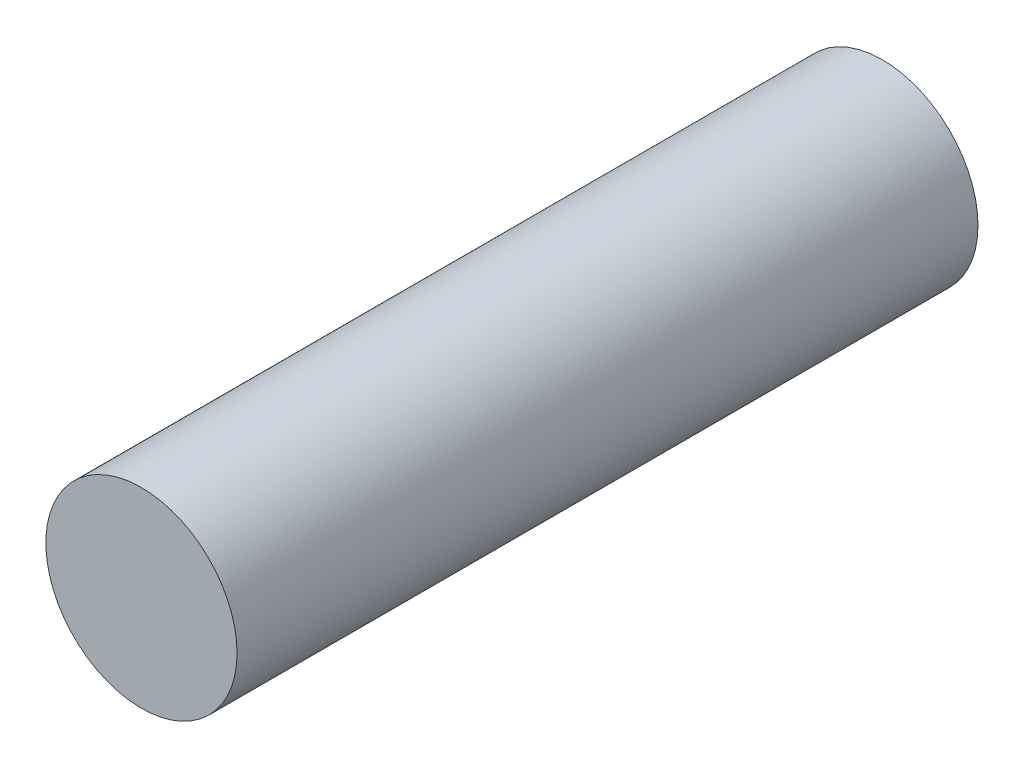
SolidWorks part; units mm, degrees
ref_plane "Front Plane" through (0, 0, 0) normal (0, 0, 1) x (1, 0, 0)
ref_plane "Top Plane" through (0, 0, 0) normal (0, 1, 0) x (1, 0, 0)
ref_plane "Right Plane" through (0, 0, 0) normal (1, 0, 0) x (0, 0, -1)
sketch "Sketch2" plane through (0, 0, 0) normal (0, 0, 1) x (1, 0, 0)
  circle A0 centre (-66.2495, 32.8843) radius 8
extrude "Boss-Extrude1" add sketch "Sketch2" along normal blind 62
